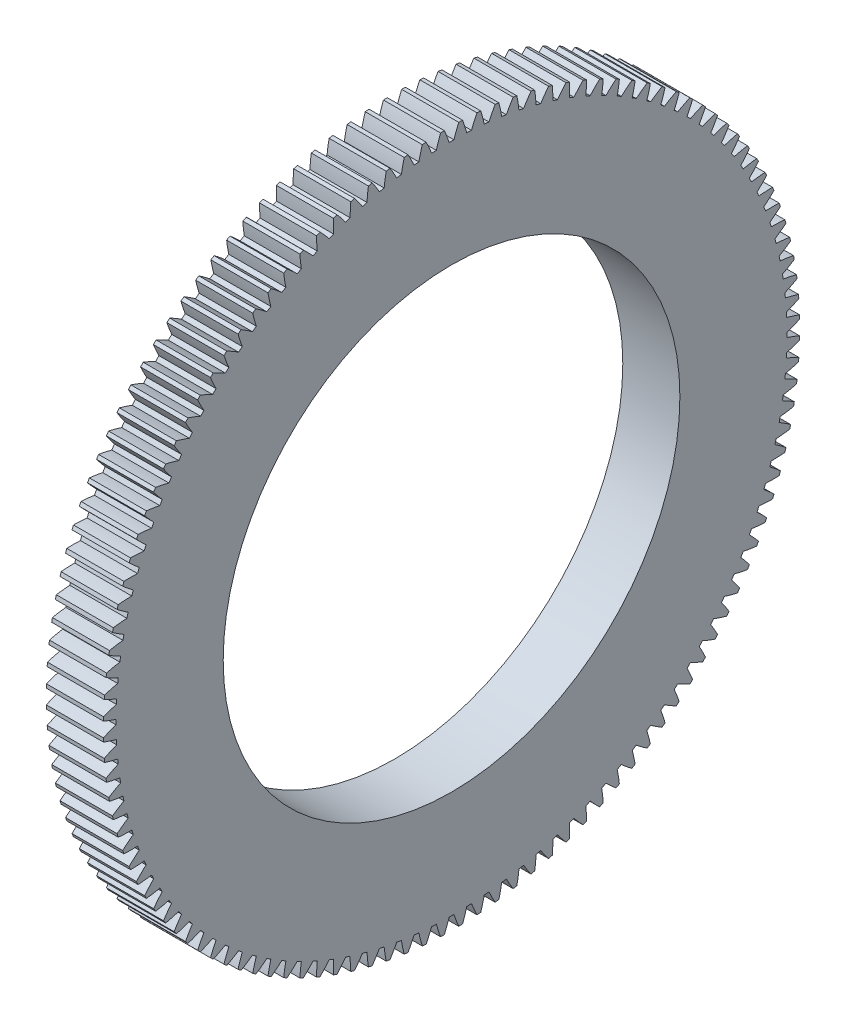
SolidWorks part; units mm, degrees
ref_plane "Plane1" through (0, 0, 0) normal (0, 0, 1) x (1, 0, 0)
ref_plane "Plane2" through (0, 0, 0) normal (0, 1, 0) x (1, 0, 0)
ref_plane "Plane3" through (0, 0, 0) normal (1, 0, 0) x (0, 0, -1)
sketch "HoldingSke" plane through (0, 0, 0) normal (0, 1, 0) x (1, 0, 0)
  line L0 (0, 0) -> (-254, -439.9409)
  line L1 (-15, 0) -> (100, 0) construction
  line L2 (0, 0) -> (-2.1039, 2.3779)
  line L3 (0, 0) -> (-11.863, 4.5341)
  line L4 (0, 0) -> (-4.318, 7.479)
  line L5 (0, 0) -> (-47.5972, -17.7524)
  line L6 (0, 0) -> (-10.5278, -7.1032)
  line L7 (-2.1039, 2.3779) -> (8.8308, 51.9871)
  line L8 (-76.2, 54.61) -> (36.6014, 54.61)
  line L9 (-71.009, 38.7566) -> (-53.1078, 45.2721)
  line L10 (-76.2, 71.12) -> (104.1128, 71.12)
  line L11 (0, 0) -> (-12.7, 0)
  line L12 (-76.2, 101.6) -> (-76.1492, 101.6)
  line L13 (24.9733, 27.94) -> (52.9518, 28.4284)
  line L14 (24.9733, 27.94) -> (25.0241, 27.9398)
  line L15 (24.9733, 27.94) -> (100.4021, 29.52)
  circle A0 centre (0, 0) radius 50.8
  circle A1 centre (0, 0) radius 38.1
  circle A2 centre (0, 0) radius 38.1
  circle A3 centre (0, 0) radius 50.8
  dimension "MHD" = 76.2
  dimension "Hub_dia" = 76.2
  dimension "Bore" = 101.6
  dimension "MBD" = 101.6
  dimension "Num_teeth" = 120
  dimension "Pitch" = 508
  dimension "Overall_len" = 50.8
  dimension "Show_teeth" = 120
  dimension "Thickness" = 12.7
  dimension "OAL" = 50.8001
  dimension "T_dim" = 112.8014
  dimension "Ap" = 20
  dimension "H" = 19.05
  dimension "Pitch_radius" = 180.3128
  dimension "Width" = 12.7
  dimension "Backlash" = 0.0508
  dimension "Addendum_fac" = 1
  dimension "Dedendum_fac" = 1.2
  dimension "Clearance_fac" = 0.2
  dimension "Dedendum_add" = 0.0508
sketch "BasProSke" plane through (0, 0, 0) normal (0, 1, 0) x (1, 0, 0)
  line L0 (-10, 0) -> (60, 0) construction
  line L1 (0, 0) -> (0, 77.47)
  line L2 (0, 0) -> (12.7, 0)
  line L3 (12.7, 0) -> (12.7, 77.47)
  line L4 (12.7, 77.47) -> (0, 77.47)
  dimension "Thickness" = 12.7
  dimension "Diameter" = 154.94
revolve "Base-Revolve" add sketch "BasProSke" angle 360 about L0
sketch "TooCutSke" plane through (0, 0, 0) normal (1, 0, 0) x (0, 0, -1)
  line L1 (0, 0) -> (0, 107) construction
  line L2 (0, 0) -> (-1.0863, 76.1923) construction
  line L3 (0, 0) -> (-3.9891, 152.3369) construction
  line L4 (-1.0863, 76.1923) -> (-1.9945, 76.1685) construction
  arc A0 (0.5305, 74.6233) -> (-0.5305, 74.6233) centre (0, 0) ccw
  arc A1 (1.616, 77.4785) -> (-1.616, 77.4785) centre (0, 0) ccw
  circle A2 centre (0, 0) radius 76.2 construction
  circle A3 centre (0, 0) radius 71.6046 construction
  arc A4 (-0.5305, 74.6233) -> (-1.616, 77.4785) centre (-29.5279, 65.2328) ccw
  arc A5 (1.616, 77.4785) -> (0.5305, 74.6233) centre (29.5279, 65.2328) ccw
  dimension "Root_dia" = 149.2504
  dimension "Overcut_dia" = 154.9908
  dimension "Pitch_dia" = 152.4
  dimension "Base_dia" = 143.2092
  dimension "Flank_rad" = 30.48
  dimension "Half_ang" = 1.5
  dimension "Half_CT" = 0.9085
extrude "ToothCut" cut sketch "TooCutSke" along normal through all
fillet "Breaks" [suppressed] radius 0.0254
fillet "RootFillets" [suppressed] radius 0.3048
pattern_circular "TeethCuts" count 120 every 3 about axis through (-10, 0, 0) along (1, 0, 0) of "ToothCut", "RootFillets", "Breaks"
sketch "HubNeaOneSke" plane through (0, 0, 0) normal (-1, 0, 0) x (0, 0, 1)
  circle A0 centre (0, 0) radius 38.1
  dimension "Diameter" = 76.2
extrude "HubNearOne" [suppressed] add sketch "HubNeaOneSke" along normal blind 38.1001
sketch "HubNeaBotSke" plane through (0, 0, 0) normal (-1, 0, 0) x (0, 0, 1)
  circle A0 centre (0, 0) radius 38.1
  dimension "Diameter" = 76.2
extrude "HubNearBoth" [suppressed] add sketch "HubNeaBotSke" along normal blind 19.05
ref_plane "FarPln" through (12.7, 0, 0) normal (1, 0, 0) x (0, 0, -1)
sketch "HubFarSke" plane through (12.7, 0, 0) normal (1, 0, 0) x (0, 0, -1)
  circle A0 centre (0, 0) radius 38.1
  dimension "Diameter" = 76.2
extrude "HubFar" [suppressed] add sketch "HubFarSke" along normal blind 19.05
sketch "BorSke" plane through (0, 0, 0) normal (1, 0, 0) x (0, 0, -1)
  circle A0 centre (0, 0) radius 50.8
  dimension "Diameter" = 101.6
extrude "Bore" cut sketch "BorSke" along normal mid plane 101.6001
sketch "KeySke" plane through (0, 0, 0) normal (1, 0, 0) x (0, 0, -1)
  line L0 (-12.7, 0) -> (-12.7, 62.0014)
  line L1 (-12.7, 62.0014) -> (12.7, 62.0014)
  line L2 (12.7, 62.0014) -> (12.7, 0)
  line L3 (0, 0) -> (0, 34) construction
  line L4 (-12.7, 0) -> (12.7, 0)
  dimension "Offset" = 62.0014
  dimension "Width" = 25.4
extrude "Keyway" [suppressed] cut sketch "KeySke" along normal mid plane 101.6001
pattern_circular "Keyway2" [suppressed] count 2 every 90 about axis through (-10, 0, 0) along (1, 0, 0)
equation "' \"Pitch@HoldingSke\" = 4"
equation "' \"Num_teeth@HoldingSke\" = 12"
equation "' \"Ap@HoldingSke\" =  20"
equation "' \"Ap@HoldingSke\" = 20"
equation "' \"Width@HoldingSke\" = 0.5"
equation "' \"Hub_dia@HoldingSke\"= 1"
equation "' \"Hub_dia@HoldingSke\" = 1"
equation "' \"Overall_len@HoldingSke\" = 1.0"
equation "' \"Bore@HoldingSke\" = 0.75"
equation "' \"T_dim@HoldingSke\" = 0.85"
equation "' \"Width@KeySke\" = 0.25"
equation "' \"Show_teeth@HoldingSke\" = 13"
equation "' \"Backlash@HoldingSke\" = 0.009"
equation "' \"Addendum_fac@HoldingSke\" = 1.0"
equation "' \"Dedendum_fac@HoldingSke\" = 1.25"
equation "' \"Dedendum_add@HoldingSke\" = 0.00005"
equation "' \"Clearance_fac@HoldingSke\" = 0.25"
equation "' \"Pitch@HoldingSke\" = 0.5"
equation "' \"Num_teeth@HoldingSke\" = 23"
equation "' \"Show_teeth@HoldingSke\" = 23"
equation "' \"Backlash@HoldingSke\" = 0.0375"
equation "\"Overcut_dia@TooCutSke\" = (\"Num_teeth@HoldingSke\" + 2 * \"Addendum_fac@HoldingSke\") / \"Pitch@HoldingSke\" + 0.002"
equation "\"Pitch_dia@TooCutSke\" = \"Num_teeth@HoldingSke\" / \"Pitch@HoldingSke\""
equation "\"Base_dia@TooCutSke\" = \"Num_teeth@HoldingSke\" / \"Pitch@HoldingSke\" * cos((\"Ap@HoldingSke\"  * 3.14159265 / 180))"
equation "\"Root_dia@TooCutSke\" = (\"Num_teeth@HoldingSke\" + 2) / \"Pitch@HoldingSke\" - 2 * (\"Addendum_fac@HoldingSke\" + \"Dedendum_fac@HoldingSke\") / \"Pitch@HoldingSke\" - \"Dedendum_add@HoldingSke\" * 2"
equation "\"Half_ang@TooCutSke\" = 180 / \"Num_teeth@HoldingSke\""
equation "\"Half_CT@TooCutSke\" = \"Num_teeth@HoldingSke\" / \"Pitch@HoldingSke\" * sin((3.14159265 / 2 / \"Num_teeth@HoldingSke\")) / 2 - 7 * \"Backlash@HoldingSke\" / 4"
equation "\"Flank_rad@TooCutSke\" = \"Num_teeth@HoldingSke\" / \"Pitch@HoldingSke\" / 5"
equation "\"Radius@RootFillets\" = \"Clearance_fac@HoldingSke\" / \"Pitch@HoldingSke\" + \"Dedendum_add@HoldingSke\""
equation "\"Break_rad@Breaks\" = 0.02 / \"Pitch@HoldingSke\""
equation "\"Thickness@HoldingSke\" = \"Width@HoldingSke\""
equation "\"OAL@HoldingSke\" = \"Thickness@HoldingSke\""
equation "\"MHD@HoldingSke\" = (\"Num_teeth@HoldingSke\" + 2) / \"Pitch@HoldingSke\" - 2 * (\"Addendum_fac@HoldingSke\" + \"Dedendum_fac@HoldingSke\")  / \"Pitch@HoldingSke\" - \"Dedendum_add@HoldingSke\" * 2"
equation "\"MBD@HoldingSke\" = (\"Num_teeth@HoldingSke\" + 2) / \"Pitch@HoldingSke\" - 2 * (\"Addendum_fac@HoldingSke\" + \"Dedendum_fac@HoldingSke\")  / \"Pitch@HoldingSke\" - \"Dedendum_add@HoldingSke\" * 2 - 0.002"
equation "\"MHD@HoldingSke\" = ((sgn( \"MHD@HoldingSke\" - \"Hub_dia@HoldingSke\" )-1)*( \"MHD@HoldingSke\" - \"Hub_dia@HoldingSke\" ))/-2+ \"Hub_dia@HoldingSke\""
equation "\"MBD@HoldingSke\" = ((sgn( \"MBD@HoldingSke\" - \"Bore@HoldingSke\" )-1)*( \"MBD@HoldingSke\" - \"Bore@HoldingSke\" ))/-2+ \"Bore@HoldingSke\""
equation "\"OAL@HoldingSke\" = ((sgn( \"OAL@HoldingSke\" - \"Overall_len@HoldingSke\" )+1)*( \"OAL@HoldingSke\" - \"Overall_len@HoldingSke\" ))/2 + \"Overall_len@HoldingSke\" + 0.000002"
equation "\"Num_teeth@TeethCuts\" = int( \"Show_teeth@HoldingSke\" ) + 1"
equation "\"Num_teeth@TeethCuts\" = ((sgn( \"Num_teeth@TeethCuts\" - \"Num_teeth@HoldingSke\" )-1)*( \"Num_teeth@TeethCuts\" - \"Num_teeth@HoldingSke\" ))/-2+ \"Num_teeth@HoldingSke\""
equation "\"Num_teeth@TeethCuts\" = ((sgn( \"Num_teeth@TeethCuts\" - 2.0)+1)*( \"Num_teeth@TeethCuts\" - 2.0))/2 +2.0"
equation "\"Angle@TeethCuts\" = 360.0 / \"Num_teeth@HoldingSke\""
equation "\"Diameter@BasProSke\" = (\"Num_teeth@HoldingSke\" + 2 * \"Addendum_fac@HoldingSke\") / \"Pitch@HoldingSke\""
equation "\"Thickness@BasProSke\"  = \"Thickness@HoldingSke\""
equation "' \"Fillet_rad@BasProSke\" =  \"Thickness@HoldingSke\" * 0.05"
equation "' \"Fillet_rad@BasProSke\" = \"Thickness@HoldingSke\" * 0.05"
equation "\"MHD@HoldingSke\" = ((sgn( \"MHD@HoldingSke\" - \"Root_dia@TooCutSke\" )-1)*( \"MHD@HoldingSke\" - \"Root_dia@TooCutSke\" ))/-2+ \"Root_dia@TooCutSke\""
equation "\"Diameter@HubNeaOneSke\" = \"MHD@HoldingSke\""
equation "\"Length@HubNearOne\" = \"OAL@HoldingSke\" - \"Thickness@BasProSke\""
equation "\"Diameter@HubNeaBotSke\" = \"MHD@HoldingSke\""
equation "\"Length@HubNearBoth\" = ( \"OAL@HoldingSke\" - \"Thickness@BasProSke\" ) / 2.0"
equation "\"Thickness@FarPln\" = \"Thickness@BasProSke\""
equation "\"Diameter@HubFarSke\" = \"MHD@HoldingSke\""
equation "\"Length@HubFar\" = ( \"OAL@HoldingSke\" - \"Thickness@BasProSke\" ) / 2.0"
equation "\"Diameter@BorSke\" = \"MBD@HoldingSke\""
equation "\"D1@Bore\" = \"OAL@HoldingSke\" * 2.0"
equation "\"D1@Keyway\" = \"OAL@HoldingSke\" * 2.0"
equation "\"Offset@KeySke\" = \"T_dim@HoldingSke\" - \"MBD@HoldingSke\" / 2.0"
